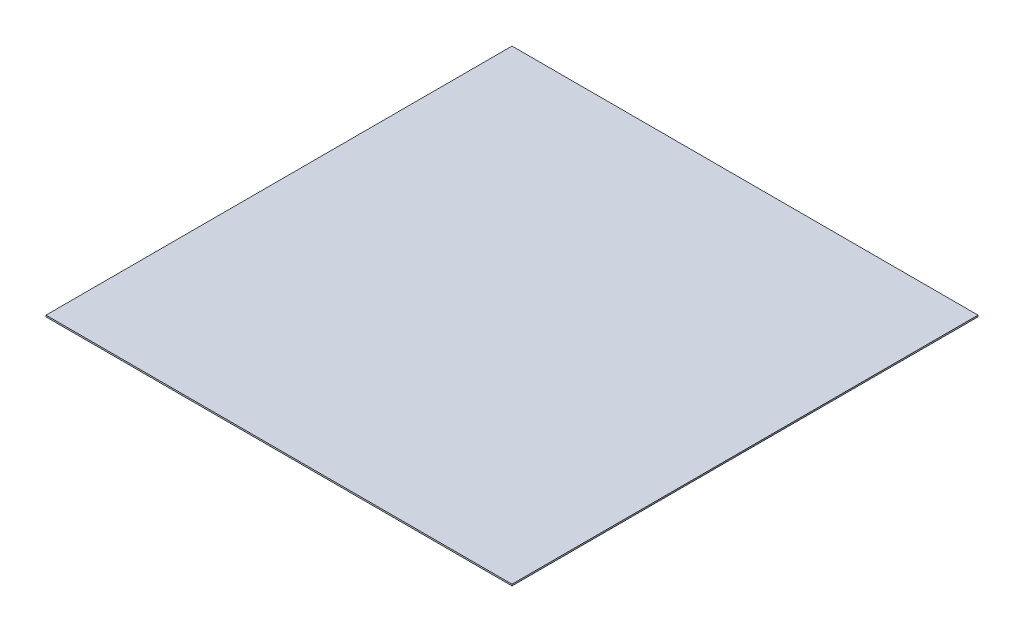
SolidWorks part; units mm, degrees
other "COLL.BOX-Boss-Extrude2"
material "Lightweight"
ref_plane "Front Plane" through (0, 0, 0) normal (0, 0, 1) x (1, 0, 0)
ref_plane "Top Plane" through (0, 0, 0) normal (0, 1, 0) x (1, 0, 0)
ref_plane "Right Plane" through (0, 0, 0) normal (1, 0, 0) x (0, 0, -1)
sketch "Sketch1" plane through (0, 0, 0) normal (0, 1, 0) x (1, 0, 0)
  line L1 (-15000, 15000) -> (15000, 15000)
  line L2 (-15000, 15000) -> (-15000, -15000)
  line L3 (-15000, -15000) -> (15000, -15000)
  line L4 (15000, 15000) -> (15000, -15000)
  line L5 (-15000, 15000) -> (15000, -15000) construction
  line L6 (-15000, -15000) -> (15000, 15000) construction
  point P0 (0, 0)
  dimension "D1" = 30000
  dimension "D2" = 30000
extrude "Boss-Extrude1" add sketch "Sketch1" along normal blind 100
sketch "Sketch2" plane through (0, 100, 0) normal (0, 1, 0) x (1, 0, 0)
  line L1 (-15000, -15000) -> (15000, -15000)
  line L2 (-15000, -15000) -> (-15000, 15000)
  line L3 (-15000, 15000) -> (15000, 15000)
  line L4 (15000, -15000) -> (15000, 15000)
extrude "Boss-Extrude2" add sketch "Sketch2" against normal up to vertex (100 mm away) separate body
